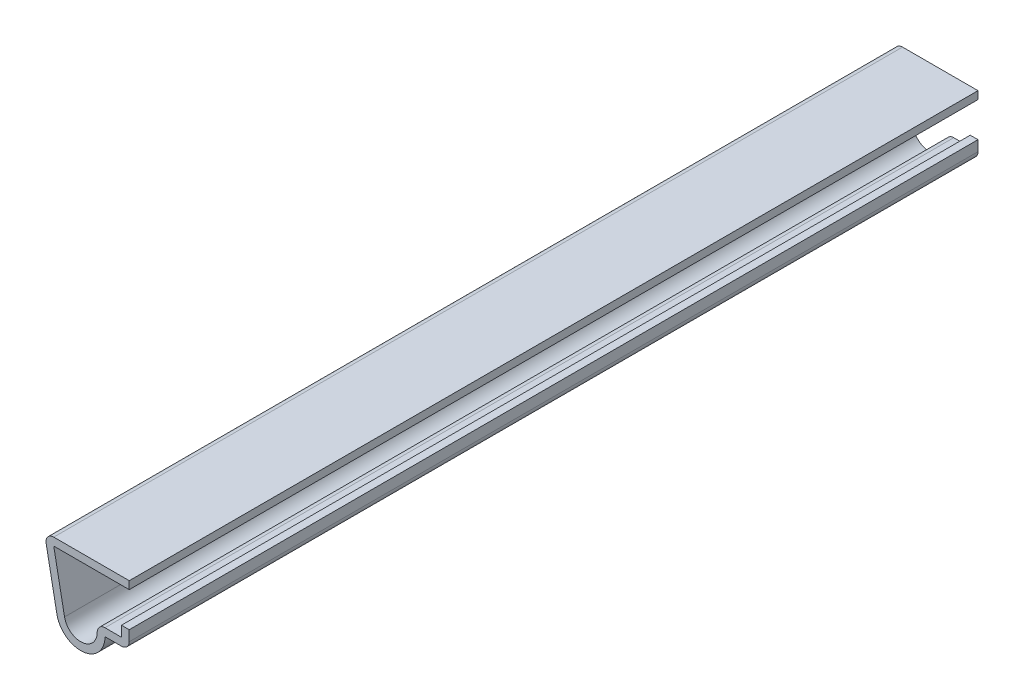
SolidWorks part; units mm, degrees
ref_plane "Front Plane" through (0, 0, 0) normal (0, 0, 1) x (1, 0, 0)
ref_plane "Top Plane" through (0, 0, 0) normal (0, 1, 0) x (1, 0, 0)
ref_plane "Right Plane" through (0, 0, 0) normal (1, 0, 0) x (0, 0, -1)
sketch "Sketch1" plane through (0, 0, 0) normal (0, 0, 1) x (1, 0, 0)
  line L0 (0, 2.3813) -> (0, 0)
  line L1 (0, 0) -> (-3.175, 0)
  line L2 (-9.4677, -0.6006) -> (-11.1125, 7.9375)
  line L3 (-11.1125, 7.9375) -> (0, 7.9375)
  arc A0 (-3.175, 0) -> (-9.4677, -0.6006) centre (-6.35, 0) cw
  point P8 (0, 0)
  point P9 (0, 2.4127)
  point P10 (-9.5446, -0.547)
  point P11 (0, 0)
  point P12 (0, 1.6593)
  dimension "D1" = 11.1125
  dimension "D2" = 11.1125
  dimension "D3" = 7.9375
  dimension "D4" = 3.175
  dimension "D5" = 2.3813
extrude "Extrude-Thin1" add sketch "Sketch1" against normal blind 111.125 thin
fillet "Fillet1" radius 1.016 3 edges at (0, 0, -55.5625) (-4.445, 1.016, -55.5625) (-11.1125, 7.9375, -55.5625)
